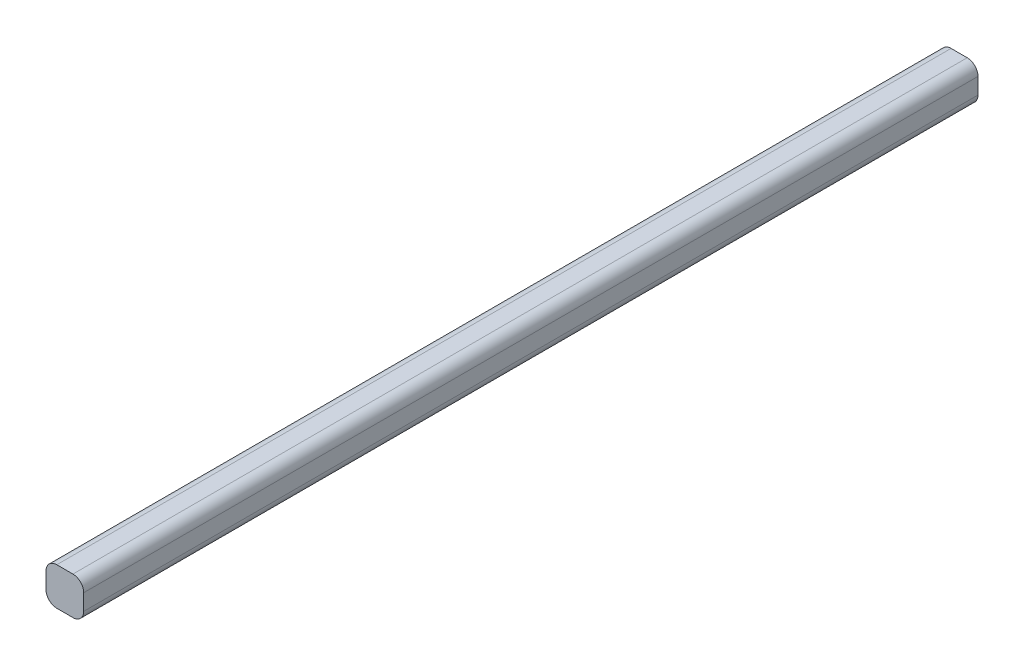
SolidWorks part; units mm, degrees
ref_plane "Plano frontal" through (0, 0, 0) normal (0, 0, 1) x (1, 0, 0)
ref_plane "Plano superior" through (0, 0, 0) normal (0, 1, 0) x (1, 0, 0)
ref_plane "Plano direito" through (0, 0, 0) normal (1, 0, 0) x (0, 0, -1)
sketch "Esboço1" plane through (0, 0, 0) normal (0, 0, 1) x (1, 0, 0)
  line L1 (0, 0) -> (35, 0)
  line L2 (0, 0) -> (0, 35)
  line L3 (0, 35) -> (35, 35)
  line L4 (35, 0) -> (35, 35)
  dimension "D1" = 35
  dimension "D2" = 35
extrude "Ressalto-extrusão1" add sketch "Esboço1" along normal blind 830
fillet "Filete1" radius 10 4 edges at (0, 0, 415) (0, 35, 415) (35, 0, 415) (35, 35, 415)
